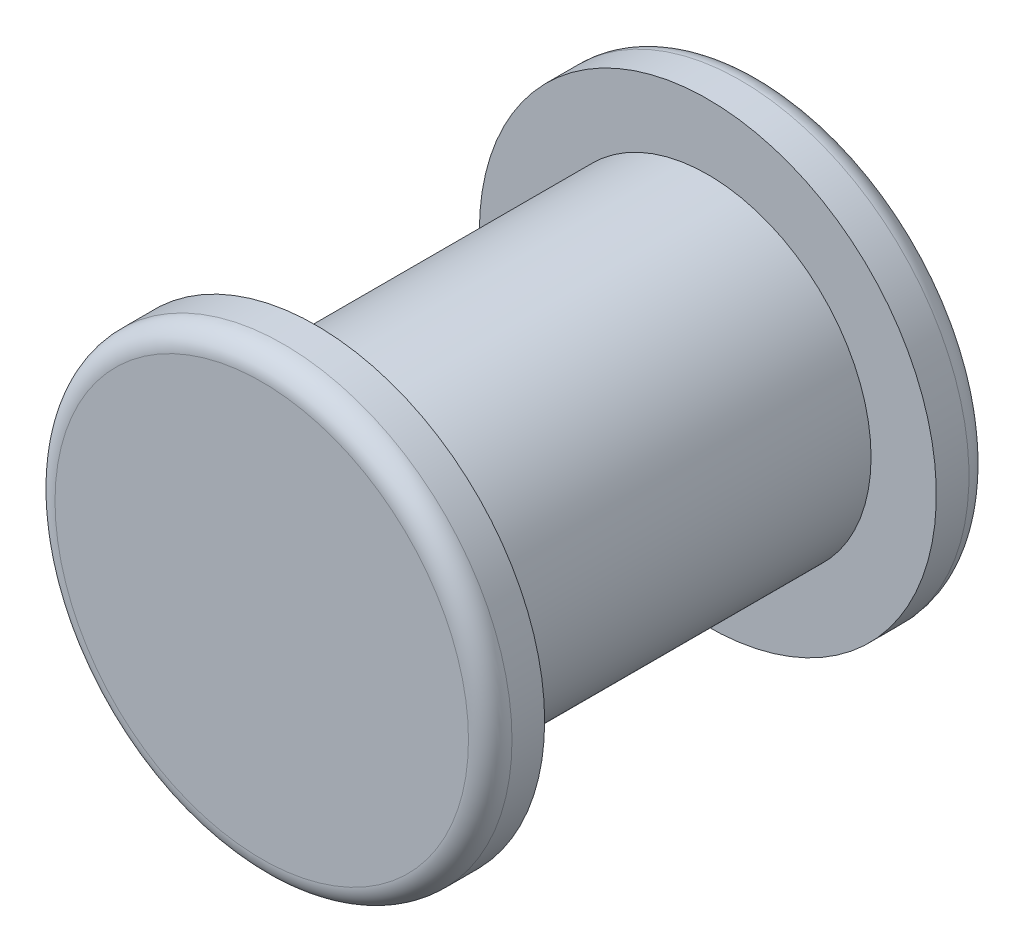
SolidWorks part; units mm, degrees
material "Wrought Stainless Steel"
ref_plane "Front Plane" through (0, 0, 0) normal (0, 0, 1) x (1, 0, 0)
ref_plane "Top Plane" through (0, 0, 0) normal (0, 1, 0) x (1, 0, 0)
ref_plane "Right Plane" through (0, 0, 0) normal (1, 0, 0) x (0, 0, -1)
sketch "Sketch1" plane through (0, 0, 0) normal (0, 0, 1) x (1, 0, 0)
  circle A0 centre (0, 0) radius 75
  dimension "D1" = 150
extrude "Boss-Extrude1" add sketch "Sketch1" along normal blind 180 contours A0
sketch "Sketch2" plane through (0, 0, 180) normal (0, 0, 1) x (1, 0, 0)
  circle A0 centre (0, 0) radius 105
  dimension "D1" = 210
extrude "Boss-Extrude2" add sketch "Sketch2" along normal blind 25
sketch "Sketch3" plane through (0, 0, 0) normal (0, 0, -1) x (-1, 0, 0)
  circle A0 centre (0, 0) radius 105
  dimension "D1" = 210
extrude "Boss-Extrude3" add sketch "Sketch3" along normal blind 25
fillet "Fillet1" radius 10 2 edges at (105, 0, 205) (-105, 0, -25)
